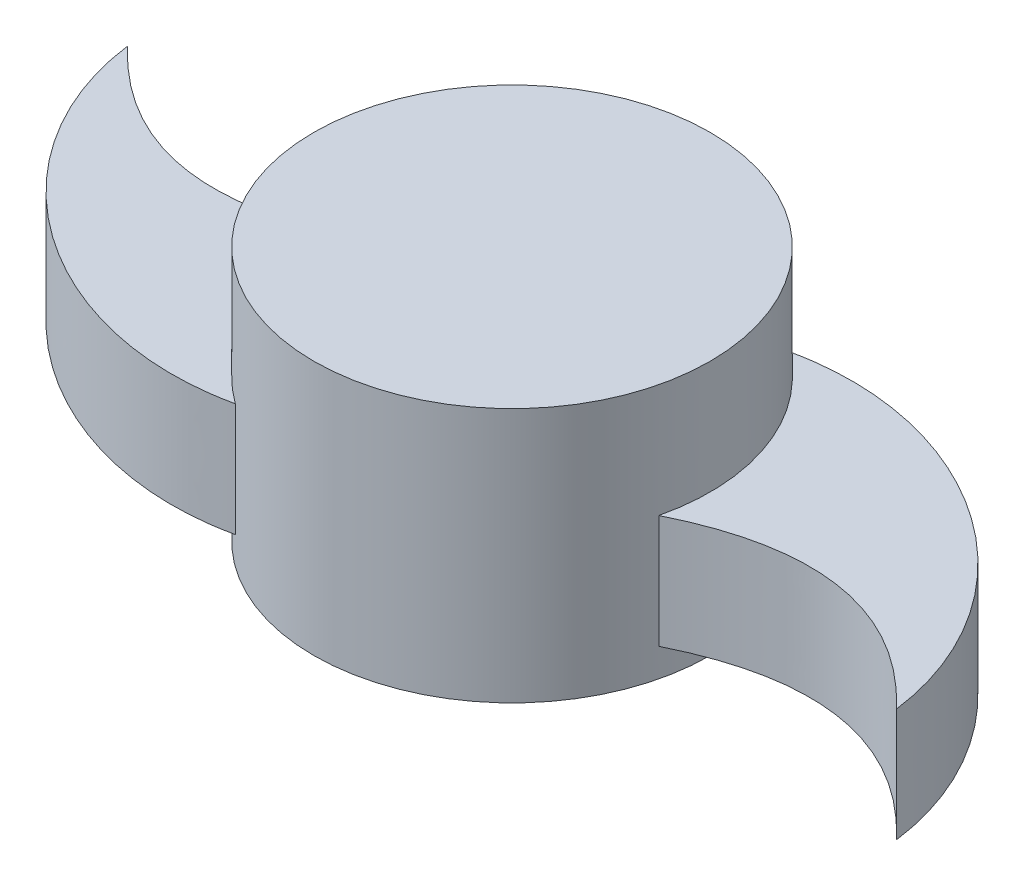
SolidWorks part; units mm, degrees
ref_plane "Front Plane" through (0, 0, 0) normal (0, 0, 1) x (1, 0, 0)
ref_plane "Top Plane" through (0, 0, 0) normal (0, 1, 0) x (1, 0, 0)
ref_plane "Right Plane" through (0, 0, 0) normal (1, 0, 0) x (0, 0, -1)
sketch "Sketch1" plane through (0, 0, 0) normal (0, 1, 0) x (1, 0, 0)
  circle A0 centre (0, 0) radius 44.45
  dimension "D1" = 88.9
extrude "Boss-Extrude1" add sketch "Sketch1" along normal blind 57.15
ref_plane "Plane1" through (0, 6.35, 0) normal (0, 1, 0) x (1, 0, 0)
sketch "Sketch3" plane through (0, 6.35, 0) normal (0, 1, 0) x (1, 0, 0)
  line L0 (-97.7949, 0) -> (100.4864, 0) construction
  line L1 (0, 55.8501) -> (0, -60.8326) construction
  circle A0 centre (0, 0) radius 44.45 construction
  arc A1 (25.9384, 36.0971) -> (43.2342, -10.3252) centre (0, 0) cw
  arc A3 (-25.9384, -36.0971) -> (-43.2342, 10.3252) centre (0, 0) cw
  spline S0 degree 3 poles (25.9384, 36.0971) (62.8493, 44.2501) (102.7892, 15.3744) (107.4715, -21.3034) knots 0 0 0 0 1 1 1 1
  spline S1 degree 2 poles (107.4715, -21.3034) (79.9424, 7.9093) (43.2342, -10.3252) knots 0 0 0 1 1 1
  spline S4 degree 2 poles (-107.4715, 21.3034) (-79.9424, -7.9093) (-43.2342, 10.3252) knots 0 0 0 1 1 1
  spline S5 degree 3 poles (-25.9384, -36.0971) (-62.8493, -44.2501) (-102.7892, -15.3744) (-107.4715, 21.3034) knots 0 0 0 0 1 1 1 1
extrude "Boss-Extrude2" add sketch "Sketch3" along normal blind 25.4
